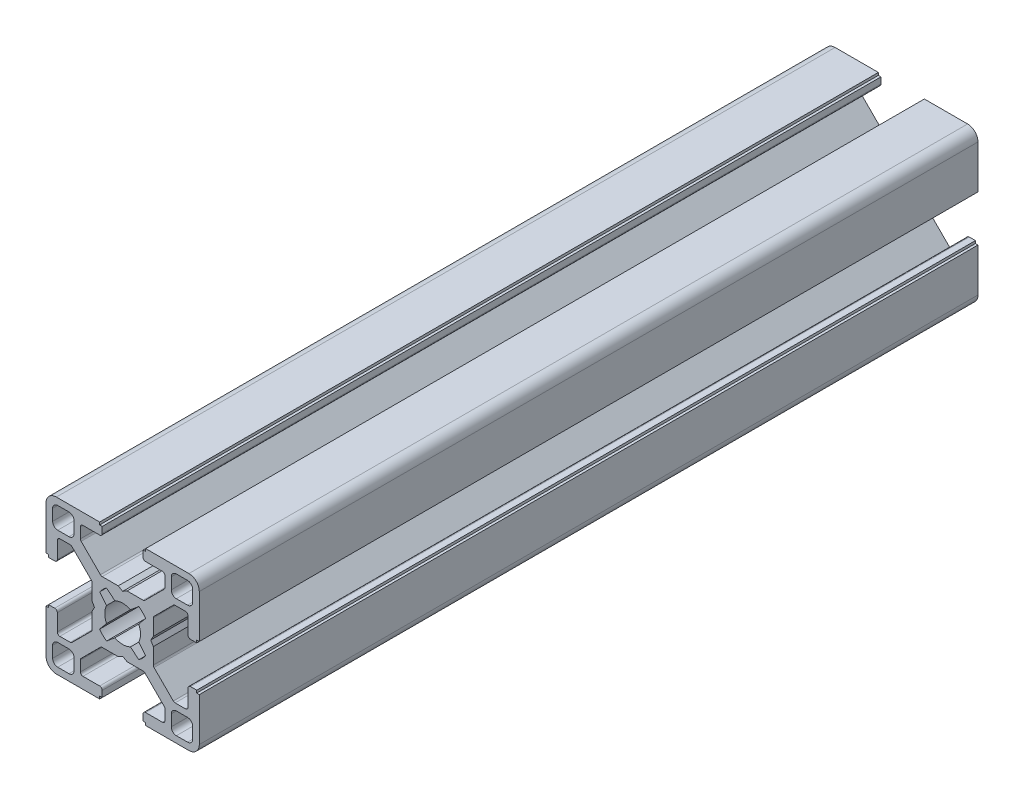
SolidWorks part; units mm, degrees
ref_plane "Front Plane" through (0, 0, 0) normal (0, 0, 1) x (1, 0, 0)
ref_plane "Top Plane" through (0, 0, 0) normal (0, 1, 0) x (1, 0, 0)
ref_plane "Right Plane" through (0, 0, 0) normal (1, 0, 0) x (0, 0, -1)
sketch "Sketch1" plane through (0, 0, 0) normal (0, 0, 1) x (1, 0, 0)
  line L0 (-15, 0) -> (15, 0) construction
  line L1 (0, -15) -> (0, 15) construction
  line L2 (-4.5, 15) -> (4.5, 15) construction
  line L3 (-4, -15) -> (4, -15) construction
  line L4 (-4.5, 15) -> (-4.5, 14.5)
  line L5 (-4.5, 14.5) -> (-4, 14.5)
  line L6 (-4, 14.5) -> (-4, 13.29)
  line L7 (-4.5, 12.79) -> (-7.7675, 12.79)
  line L8 (-8.2675, 12.29) -> (-8.2675, 10.2707)
  line L9 (-8.1211, 9.9171) -> (-4.3504, 6.1464)
  line L10 (-3.9968, 6) -> (0, 6)
  line L11 (0, 0) -> (-15, 15) construction
  line L12 (-4.5, 15) -> (-12.968, 15)
  line L14 (-12.705, 9.5135) -> (-10.5135, 9.5135)
  line L15 (-13.705, 10.5135) -> (-13.705, 12.705)
  line L16 (-12.705, 13.705) -> (-10.5135, 13.705)
  line L17 (-9.5135, 10.5135) -> (-9.5135, 12.705)
  line L18 (-13.705, 9.5135) -> (-9.5135, 13.705) construction
  line L19 (-13.705, 13.705) -> (-9.5135, 9.5135) construction
  line L20 (-3.1568, 4.5038) -> (-1.5303, 3.1477) construction
  line L21 (-4.5038, 3.1568) -> (-3.1477, 1.5303) construction
  line L22 (-6, 3.9968) -> (-6, 0)
  line L23 (-9.9171, 8.1211) -> (-6.1464, 4.3504)
  line L24 (-15, 4.5) -> (-15, 12.968)
  line L25 (-12.29, 8.2675) -> (-10.2707, 8.2675)
  line L26 (-12.79, 4.5) -> (-12.79, 7.7675)
  line L27 (-14.5, 4) -> (-13.29, 4)
  line L28 (-14.5, 4.5) -> (-14.5, 4)
  line L29 (-15, 4.5) -> (-14.5, 4.5)
  circle A0 centre (0, 0) radius 3.5
  arc A1 (-12.968, 15) -> (-15, 12.968) centre (-12.968, 12.968) ccw
  circle A2 centre (0, 0) radius 5.5 construction
  arc A3 (-10.5135, 9.5135) -> (-9.5135, 10.5135) centre (-10.5135, 10.5135) ccw
  arc A4 (-13.705, 12.705) -> (-12.705, 13.705) centre (-12.705, 12.705) cw
  arc A5 (-10.5135, 13.705) -> (-9.5135, 12.705) centre (-10.5135, 12.705) cw
  arc A6 (-12.705, 9.5135) -> (-13.705, 10.5135) centre (-12.705, 10.5135) cw
  arc A7 (-12.79, 4.5) -> (-13.29, 4) centre (-13.29, 4.5) cw
  arc A8 (-12.29, 8.2675) -> (-12.79, 7.7675) centre (-12.29, 7.7675) ccw
  arc A9 (-9.9171, 8.1211) -> (-10.2707, 8.2675) centre (-10.2707, 7.7675) ccw
  arc A10 (-6, 3.9968) -> (-6.1464, 4.3504) centre (-6.5, 3.9968) ccw
  arc A11 (-4.3504, 6.1464) -> (-3.9968, 6) centre (-3.9968, 6.5) ccw
  arc A12 (-4, 13.29) -> (-4.5, 12.79) centre (-4.5, 13.29) cw
  arc A13 (-7.7675, 12.79) -> (-8.2675, 12.29) centre (-7.7675, 12.29) ccw
  arc A14 (-8.2675, 10.2707) -> (-8.1211, 9.9171) centre (-7.7675, 10.2707) ccw
  point P4 (0, 0)
  point P8 (0, 0)
  point P13 (0, 15)
  point P15 (0, -15)
  point P16 (0, 6)
  point P23 (-11.6092, 11.6093)
  point P26 (0, 6)
  point P62 (-12.79, 4)
  point P65 (-12.79, 8.2675)
  point P68 (-10.0636, 8.2675)
  point P71 (-6, 4.2039)
  point P74 (-4.2039, 6)
  point P77 (-4, 12.79)
  point P80 (-8.2675, 12.79)
  point P83 (-8.2675, 10.0636)
  dimension "Center Hole Diameter" = 7
  dimension "D11" = 2.032
  dimension "D9" = 11
  dimension "D13" = 1
  dimension "D14" = 0.5
  dimension "Rail Height" = 30
  dimension "Rail Width" = 30
  dimension "T-Slot Width" = 8
  dimension "T-Slot Depth" = 9
  dimension "D1" = 9
  dimension "D2" = 45
  dimension "D3" = 8
  dimension "D4" = 2.21
  dimension "D5" = 16.535
  dimension "D7" = 2.54
  dimension "D6" = 1.295
  dimension "D8" = 1.246
  dimension "D10" = 10.36
  dimension "D12" = 1.905
sketch "Sketch2" plane through (0, 0, 0) normal (1, 0, 0) x (0, 0, -1)
  line L0 (-76.2, 0) -> (76.2, 0) construction
  line L2 (0, -15) -> (0, 15) construction
  line L3 (0, -15) -> (0, 15) construction
  line L4 (-76.2, -15) -> (-76.2, 15) construction
  line L5 (76.2, -15) -> (76.2, 15) construction
  point P0 (-38.7, 0)
  point P3 (0, 0)
  point P4 (38.7, 0)
  point P12 (-76.2, 0)
  point P14 (76.2, 0)
  dimension "Length" = 152.4
  dimension "D1" = 37.5
sketch "Sketch3" plane through (0, 0, 0) normal (0, 0, 1) x (1, 0, 0)
  line L0 (-4.5038, 3.1568) -> (-3.1477, 1.5303)
  line L1 (0, 3.5) -> (0, 5.5)
  line L2 (-5.5, 0) -> (-3.5, 0)
  line L7 (-6, 3.9968) -> (-6, 0) construction
  line L31 (-9.9171, 8.1211) -> (-6.1464, 4.3504) construction
  line L117 (-12.29, 8.2675) -> (-10.2707, 8.2675) construction
  line L118 (-12.79, 4.5) -> (-12.79, 7.7675) construction
  line L157 (-12.705, 9.5135) -> (-10.5135, 9.5135)
  line L158 (-9.5135, 10.5135) -> (-9.5135, 12.705)
  line L163 (-10.5135, 13.705) -> (-12.705, 13.705)
  line L164 (-13.705, 12.705) -> (-13.705, 10.5135)
  line L165 (-12.705, 9.5135) -> (-10.5135, 9.5135)
  line L166 (-9.5135, 10.5135) -> (-9.5135, 12.705)
  line L167 (-10.5135, 13.705) -> (-12.705, 13.705)
  line L168 (-13.705, 12.705) -> (-13.705, 10.5135)
  line L169 (-14.5, 4) -> (-13.29, 4) construction
  line L170 (-14.5, 4.5) -> (-14.5, 4) construction
  line L171 (-15, 4.5) -> (-14.5, 4.5) construction
  line L172 (-15, 4.5) -> (-15, 12.968) construction
  line L173 (-4.5, 15) -> (-12.968, 15) construction
  line L174 (-4.5, 15) -> (-4.5, 14.5) construction
  line L175 (-4.5, 14.5) -> (-4, 14.5) construction
  line L176 (-4, 14.5) -> (-4, 13.29) construction
  line L177 (-4.5, 12.79) -> (-7.7675, 12.79) construction
  line L178 (-8.2675, 12.29) -> (-8.2675, 10.2707) construction
  line L179 (-8.1211, 9.9171) -> (-4.3504, 6.1464) construction
  line L180 (-3.9968, 6) -> (0, 6) construction
  line L181 (-6, 3.9968) -> (-6, 0.866)
  line L182 (-9.9171, 8.1211) -> (-6.1464, 4.3504)
  line L183 (-12.29, 8.2675) -> (-10.2707, 8.2675)
  line L184 (-12.79, 4.5) -> (-12.79, 7.7675)
  line L185 (-14.5, 4) -> (-13.29, 4)
  line L186 (-14.5, 4.5) -> (-14.5, 4)
  line L187 (-15, 4.5) -> (-14.5, 4.5)
  line L188 (-15, 4.5) -> (-15, 12.968)
  line L189 (-4.5, 15) -> (-12.968, 15)
  line L190 (-4.5, 15) -> (-4.5, 14.5)
  line L191 (-4.5, 14.5) -> (-4, 14.5)
  line L192 (-4, 14.5) -> (-4, 13.29)
  line L193 (-4.5, 12.79) -> (-7.7675, 12.79)
  line L194 (-8.2675, 12.29) -> (-8.2675, 10.2707)
  line L195 (-8.1211, 9.9171) -> (-4.3504, 6.1464)
  line L196 (-3.9968, 6) -> (-0.866, 6)
  line L197 (-0.866, 6) -> (0, 5.5)
  line L198 (0, -15) -> (0, 15) construction
  line L199 (0, 0) -> (-15, 15) construction
  line L200 (0, 0) -> (-15, 15) construction
  line L201 (-3.1568, 4.5038) -> (-1.5303, 3.1477) construction
  line L202 (-3.1568, 4.5038) -> (-1.5303, 3.1477)
  line L203 (-6, 0.866) -> (-5.5, 0)
  line L204 (-15, 0) -> (15, 0) construction
  line L205 (-15, 0) -> (15, 0) construction
  line L206 (0, -15) -> (0, 15) construction
  arc A0 (-3.5, 0) -> (-3.1477, 1.5303) centre (0, 0) cw
  arc A10 (-6, 3.9968) -> (-6.1464, 4.3504) centre (-6.5, 3.9968) ccw construction
  circle A16 centre (0, 0) radius 3.5
  arc A18 (0, 3.5) -> (-1.5303, 3.1477) centre (0, 0) ccw
  arc A20 (-9.9171, 8.1211) -> (-10.2707, 8.2675) centre (-10.2707, 7.7675) ccw construction
  arc A22 (-12.29, 8.2675) -> (-12.79, 7.7675) centre (-12.29, 7.7675) ccw construction
  arc A28 (-13.29, 4) -> (-12.79, 4.5) centre (-13.29, 4.5) ccw construction
  arc A29 (-10.5135, 9.5135) -> (-9.5135, 10.5135) centre (-10.5135, 10.5135) ccw
  arc A30 (-9.5135, 12.705) -> (-10.5135, 13.705) centre (-10.5135, 12.705) ccw
  arc A31 (-12.705, 13.705) -> (-13.705, 12.705) centre (-12.705, 12.705) ccw
  arc A32 (-13.705, 10.5135) -> (-12.705, 9.5135) centre (-12.705, 10.5135) ccw
  arc A33 (-10.5135, 9.5135) -> (-9.5135, 10.5135) centre (-10.5135, 10.5135) ccw
  arc A34 (-9.5135, 12.705) -> (-10.5135, 13.705) centre (-10.5135, 12.705) ccw
  arc A35 (-12.705, 13.705) -> (-13.705, 12.705) centre (-12.705, 12.705) ccw
  arc A36 (-13.705, 10.5135) -> (-12.705, 9.5135) centre (-12.705, 10.5135) ccw
  arc A37 (-12.968, 15) -> (-15, 12.968) centre (-12.968, 12.968) ccw construction
  arc A38 (-4.5, 12.79) -> (-4, 13.29) centre (-4.5, 13.29) ccw construction
  arc A39 (-7.7675, 12.79) -> (-8.2675, 12.29) centre (-7.7675, 12.29) ccw construction
  arc A40 (-8.2675, 10.2707) -> (-8.1211, 9.9171) centre (-7.7675, 10.2707) ccw construction
  arc A41 (-4.3504, 6.1464) -> (-3.9968, 6) centre (-3.9968, 6.5) ccw construction
  arc A42 (-6, 3.9968) -> (-6.1464, 4.3504) centre (-6.5, 3.9968) ccw
  arc A43 (-9.9171, 8.1211) -> (-10.2707, 8.2675) centre (-10.2707, 7.7675) ccw
  arc A44 (-12.29, 8.2675) -> (-12.79, 7.7675) centre (-12.29, 7.7675) ccw
  arc A45 (-13.29, 4) -> (-12.79, 4.5) centre (-13.29, 4.5) ccw
  arc A46 (-12.968, 15) -> (-15, 12.968) centre (-12.968, 12.968) ccw
  arc A47 (-4.5, 12.79) -> (-4, 13.29) centre (-4.5, 13.29) ccw
  arc A48 (-7.7675, 12.79) -> (-8.2675, 12.29) centre (-7.7675, 12.29) ccw
  arc A49 (-8.2675, 10.2707) -> (-8.1211, 9.9171) centre (-7.7675, 10.2707) ccw
  arc A50 (-4.3504, 6.1464) -> (-3.9968, 6) centre (-3.9968, 6.5) ccw
  circle A51 centre (0, 0) radius 5.5 construction
  arc A52 (-3.1568, 4.5038) -> (-4.5038, 3.1568) centre (0, 0) ccw
  dimension "D3" = 60
  dimension "D4" = 60
  dimension "D1" = 0
  dimension "D2" = 0
extrude "Boss-Extrude1" add sketch "Sketch3" along normal mid plane 152.4
pattern_circular "CirPattern1" count 4 over 360 about axis through (0, 0, 0) along (0, 0, 1) of "Boss-Extrude1"
ref_plane "Contact Plane1" through (15, 0, 0) normal (1, 0, 0) x (0, 0, -1)
ref_plane "Contact Plane2" through (0, -15, 0) normal (0, 1, 0) x (1, 0, 0)
ref_plane "Contact Plane3" through (-15, 0, 0) normal (1, 0, 0) x (0, 0, -1)
ref_plane "Contact Plane4" through (0, 15, 0) normal (0, 1, 0) x (1, 0, 0)
equation "\"D1@Sketch2\" = \"Rail Height@Sketch1\" * 1.25"
equation "\"D1@Sketch1\"=\"T-Slot Width@Sketch1\"+1mm"
equation "\"D3@Sketch1\"=\"T-Slot Width@Sketch1\""
equation "\"D1@Boss-Extrude1\"=\"Length@Sketch2\""
